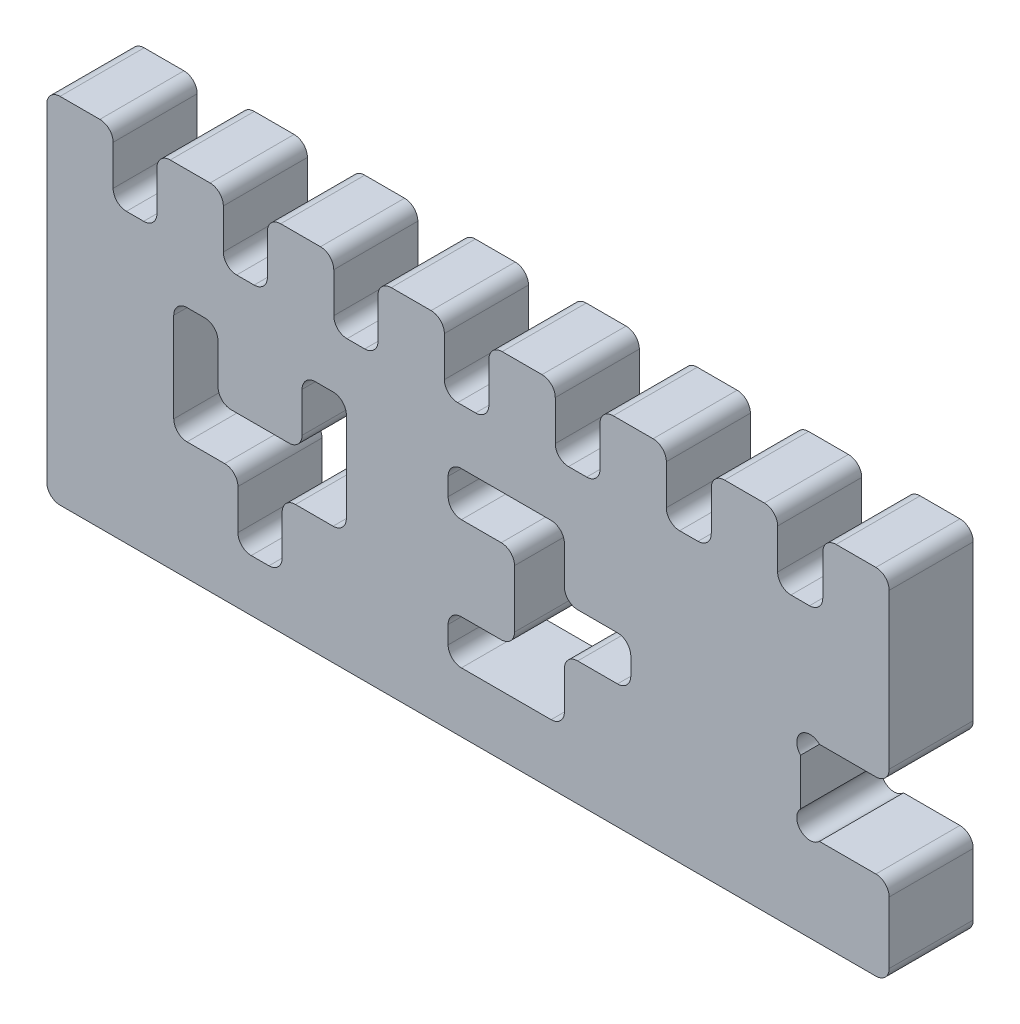
SolidWorks part; units mm, degrees
ref_plane "Front Plane" through (0, 0, 0) normal (0, 0, 1) x (1, 0, 0)
ref_plane "Top Plane" through (0, 0, 0) normal (0, 1, 0) x (1, 0, 0)
ref_plane "Right Plane" through (0, 0, 0) normal (1, 0, 0) x (0, 0, -1)
sketch "Sketch1" plane through (0, 0, 0) normal (0, 0, 1) x (1, 0, 0)
  line L53 (18, 65) -> (21.9, 65)
  line L55 (0, 3) -> (0, 77)
  line L56 (3, 80) -> (12, 80)
  line L59 (15, 77) -> (15, 68)
  line L61 (24.9, 77) -> (24.9, 68)
  line L121 (27.9, 80) -> (36.9, 80)
  line L122 (39.9, 77) -> (39.9, 68)
  line L124 (49.85, 77) -> (49.85, 68)
  line L130 (52.85, 80) -> (61.85, 80)
  line L131 (64.85, 77) -> (64.85, 68)
  line L133 (187.35, 0) -> (3, 0)
  line L134 (67.85, 65) -> (71.85, 65)
  line L135 (74.85, 77) -> (74.85, 68)
  line L136 (92.85, 65) -> (96.9, 65)
  line L137 (117.9, 65) -> (122, 65)
  line L138 (143, 65) -> (147.15, 65)
  line L139 (77.85, 80) -> (86.85, 80)
  line L140 (89.85, 77) -> (89.85, 68)
  line L141 (168.15, 65) -> (172.35, 65)
  line L142 (99.9, 77) -> (99.9, 68)
  line L144 (42.9, 65) -> (46.85, 65)
  line L145 (190.35, 17) -> (190.35, 3)
  line L146 (187.35, 39) -> (174.5926, 39)
  line L148 (102.9, 80) -> (111.9, 80)
  line L149 (114.9, 77) -> (114.9, 68)
  line L150 (187.35, 20) -> (174.5926, 20)
  line L151 (125, 77) -> (125, 68)
  line L152 (170.35, 34.7574) -> (170.35, 24.2426)
  line L153 (170.35, 20) -> (174.5926, 24.2426) construction
  line L154 (170.35, 39) -> (172.4713, 36.8787) construction
  line L156 (31.6949, 53.008) -> (35.6949, 53.008)
  line L157 (128, 80) -> (137, 80)
  line L158 (140, 77) -> (140, 68)
  line L159 (28.6949, 50.008) -> (28.6949, 41.008)
  line L160 (150.15, 77) -> (150.15, 68)
  line L162 (38.6949, 50.008) -> (38.6949, 41.008)
  line L166 (153.15, 80) -> (162.15, 80)
  line L167 (165.15, 77) -> (165.15, 68)
  line L169 (175.35, 77) -> (175.35, 68)
  line L170 (41.6949, 38.008) -> (54.6949, 38.008)
  line L173 (48.1949, 38.008) -> (48.1949, 53.008) construction
  line L175 (178.35, 80) -> (187.35, 80)
  line L176 (190.35, 77) -> (190.35, 42)
  line L178 (28.6949, 41.008) -> (28.6949, 29.7363)
  line L181 (67.6949, 41.008) -> (67.6949, 29.7363)
  line L183 (57.6949, 50.008) -> (57.6949, 41.008)
  line L184 (67.6949, 50.008) -> (67.6949, 41.008)
  line L185 (64.6949, 53.008) -> (60.6949, 53.008)
  line L188 (53.1949, 23.7363) -> (53.1949, 14.7363)
  line L189 (50.1949, 11.7363) -> (46.1949, 11.7363)
  line L190 (43.1949, 23.7363) -> (43.1949, 14.7363)
  line L193 (56.1949, 26.7363) -> (64.6949, 26.7363)
  line L195 (31.6949, 26.7363) -> (40.1949, 26.7363)
  line L197 (90.6949, 16.508) -> (90.6949, 20.508)
  line L198 (93.6949, 13.508) -> (102.6949, 13.508)
  line L199 (93.6949, 23.508) -> (102.6949, 23.508)
  line L200 (105.6949, 26.508) -> (105.6949, 39.508)
  line L201 (102.6949, 13.508) -> (113.9666, 13.508)
  line L202 (102.6949, 52.508) -> (113.9666, 52.508)
  line L203 (93.6949, 42.508) -> (102.6949, 42.508)
  line L204 (93.6949, 52.508) -> (102.6949, 52.508)
  line L205 (90.6949, 49.508) -> (90.6949, 45.508)
  line L206 (119.9666, 38.008) -> (128.9666, 38.008)
  line L207 (131.9666, 35.008) -> (131.9666, 31.008)
  line L208 (119.9666, 28.008) -> (128.9666, 28.008)
  line L209 (116.9666, 41.008) -> (116.9666, 49.508)
  line L210 (116.9666, 16.508) -> (116.9666, 25.008)
  line L211 (105.6949, 33.008) -> (131.9666, 33.008) construction
  arc A0 (12, 80) -> (15, 77) centre (12, 77) cw
  arc A1 (190.35, 3) -> (187.35, 0) centre (187.35, 3) cw
  arc A2 (3, 0) -> (0, 3) centre (3, 3) cw
  arc A3 (0, 77) -> (3, 80) centre (3, 77) cw
  arc A4 (187.35, 80) -> (190.35, 77) centre (187.35, 77) cw
  arc A5 (175.35, 77) -> (178.35, 80) centre (178.35, 77) cw
  arc A6 (175.35, 68) -> (172.35, 65) centre (172.35, 68) cw
  arc A7 (165.15, 68) -> (168.15, 65) centre (168.15, 68) ccw
  arc A8 (162.15, 80) -> (165.15, 77) centre (162.15, 77) cw
  arc A9 (150.15, 77) -> (153.15, 80) centre (153.15, 77) cw
  arc A10 (150.15, 68) -> (147.15, 65) centre (147.15, 68) cw
  arc A11 (137, 80) -> (140, 77) centre (137, 77) cw
  arc A12 (140, 68) -> (143, 65) centre (143, 68) ccw
  arc A13 (125, 77) -> (128, 80) centre (128, 77) cw
  arc A14 (125, 68) -> (122, 65) centre (122, 68) cw
  arc A15 (114.9, 68) -> (117.9, 65) centre (117.9, 68) ccw
  arc A16 (111.9, 80) -> (114.9, 77) centre (111.9, 77) cw
  arc A17 (99.9, 77) -> (102.9, 80) centre (102.9, 77) cw
  arc A18 (99.9, 68) -> (96.9, 65) centre (96.9, 68) cw
  arc A19 (89.85, 68) -> (92.85, 65) centre (92.85, 68) ccw
  arc A20 (86.85, 80) -> (89.85, 77) centre (86.85, 77) cw
  arc A21 (74.85, 77) -> (77.85, 80) centre (77.85, 77) cw
  arc A22 (74.85, 68) -> (71.85, 65) centre (71.85, 68) cw
  arc A23 (64.85, 68) -> (67.85, 65) centre (67.85, 68) ccw
  arc A24 (61.85, 80) -> (64.85, 77) centre (61.85, 77) cw
  arc A25 (49.85, 77) -> (52.85, 80) centre (52.85, 77) cw
  arc A26 (49.85, 68) -> (46.85, 65) centre (46.85, 68) cw
  arc A27 (39.9, 68) -> (42.9, 65) centre (42.9, 68) ccw
  arc A28 (21.9, 65) -> (24.9, 68) centre (21.9, 68) ccw
  arc A29 (36.9, 80) -> (39.9, 77) centre (36.9, 77) cw
  arc A30 (27.9, 80) -> (24.9, 77) centre (27.9, 77) ccw
  arc A31 (18, 65) -> (15, 68) centre (18, 68) cw
  arc A32 (174.5926, 39) -> (170.35, 34.7574) centre (172.4713, 36.8787) ccw
  arc A33 (170.35, 24.2426) -> (174.5926, 20) centre (172.4713, 22.1213) ccw
  arc A34 (190.35, 17) -> (187.35, 20) centre (187.35, 17) ccw
  arc A35 (187.35, 39) -> (190.35, 42) centre (187.35, 42) ccw
  arc A37 (41.6949, 38.008) -> (38.6949, 41.008) centre (41.6949, 41.008) cw
  arc A38 (35.6949, 53.008) -> (38.6949, 50.008) centre (35.6949, 50.008) cw
  arc A41 (31.6949, 53.008) -> (28.6949, 50.008) centre (31.6949, 50.008) ccw
  arc A42 (64.6949, 53.008) -> (67.6949, 50.008) centre (64.6949, 50.008) cw
  arc A43 (60.6949, 53.008) -> (57.6949, 50.008) centre (60.6949, 50.008) ccw
  arc A44 (54.6949, 38.008) -> (57.6949, 41.008) centre (54.6949, 41.008) ccw
  arc A45 (64.6949, 26.7363) -> (67.6949, 29.7363) centre (64.6949, 29.7363) ccw
  arc A46 (56.1949, 26.7363) -> (53.1949, 23.7363) centre (56.1949, 23.7363) ccw
  arc A47 (53.1949, 14.7363) -> (50.1949, 11.7363) centre (50.1949, 14.7363) cw
  arc A48 (46.1949, 11.7363) -> (43.1949, 14.7363) centre (46.1949, 14.7363) cw
  arc A49 (40.1949, 26.7363) -> (43.1949, 23.7363) centre (40.1949, 23.7363) cw
  arc A50 (28.6949, 29.7363) -> (31.6949, 26.7363) centre (31.6949, 29.7363) ccw
  arc A51 (105.6949, 26.508) -> (102.6949, 23.508) centre (102.6949, 26.508) cw
  arc A52 (90.6949, 20.508) -> (93.6949, 23.508) centre (93.6949, 20.508) cw
  arc A53 (90.6949, 16.508) -> (93.6949, 13.508) centre (93.6949, 16.508) ccw
  arc A54 (90.6949, 49.508) -> (93.6949, 52.508) centre (93.6949, 49.508) cw
  arc A55 (90.6949, 45.508) -> (93.6949, 42.508) centre (93.6949, 45.508) ccw
  arc A56 (105.6949, 39.508) -> (102.6949, 42.508) centre (102.6949, 39.508) ccw
  arc A57 (116.9666, 49.508) -> (113.9666, 52.508) centre (113.9666, 49.508) ccw
  arc A58 (116.9666, 41.008) -> (119.9666, 38.008) centre (119.9666, 41.008) ccw
  arc A59 (128.9666, 38.008) -> (131.9666, 35.008) centre (128.9666, 35.008) cw
  arc A60 (131.9666, 31.008) -> (128.9666, 28.008) centre (128.9666, 31.008) cw
  arc A61 (116.9666, 25.008) -> (119.9666, 28.008) centre (119.9666, 25.008) cw
  arc A62 (113.9666, 13.508) -> (116.9666, 16.508) centre (113.9666, 16.508) ccw
  point P14 (0, 0)
  point P19 (0, 80)
  point P24 (190.35, 80)
  point P29 (175.35, 80)
  point P35 (175.35, 65)
  point P41 (165.15, 65)
  point P47 (165.15, 80)
  point P56 (150.15, 80)
  point P60 (150.15, 65)
  point P65 (140, 80)
  point P69 (140, 65)
  point P72 (125, 80)
  point P75 (125, 65)
  point P78 (114.9, 65)
  point P81 (114.9, 80)
  point P84 (99.9, 80)
  point P91 (89.85, 80)
  point P94 (74.85, 80)
  point P101 (64.85, 80)
  point P104 (49.85, 80)
  point P113 (39.9, 80)
  point P116 (24.9, 80)
  point P129 (48.1949, 11.7363)
  point P133 (105.6949, 38.008)
  point P140 (190.35, 39)
  point P154 (38.6949, 53.008)
  point P161 (28.6949, 53.008)
  point P170 (67.6949, 26.7363)
  point P176 (53.1949, 11.7363)
  point P179 (43.1949, 11.7363)
  point P185 (28.6949, 26.7363)
  point P211 (116.9666, 52.508)
  point P224 (116.9666, 13.508)
  point P225 (131.9666, 38.008)
extrude "Boss-Extrude1" add sketch "Sketch1" along normal blind 19
equation "\"space\"=15"
equation "\"finger_length\"=15"
equation "\"D31@Sketch1\"=\"finger_length\""
